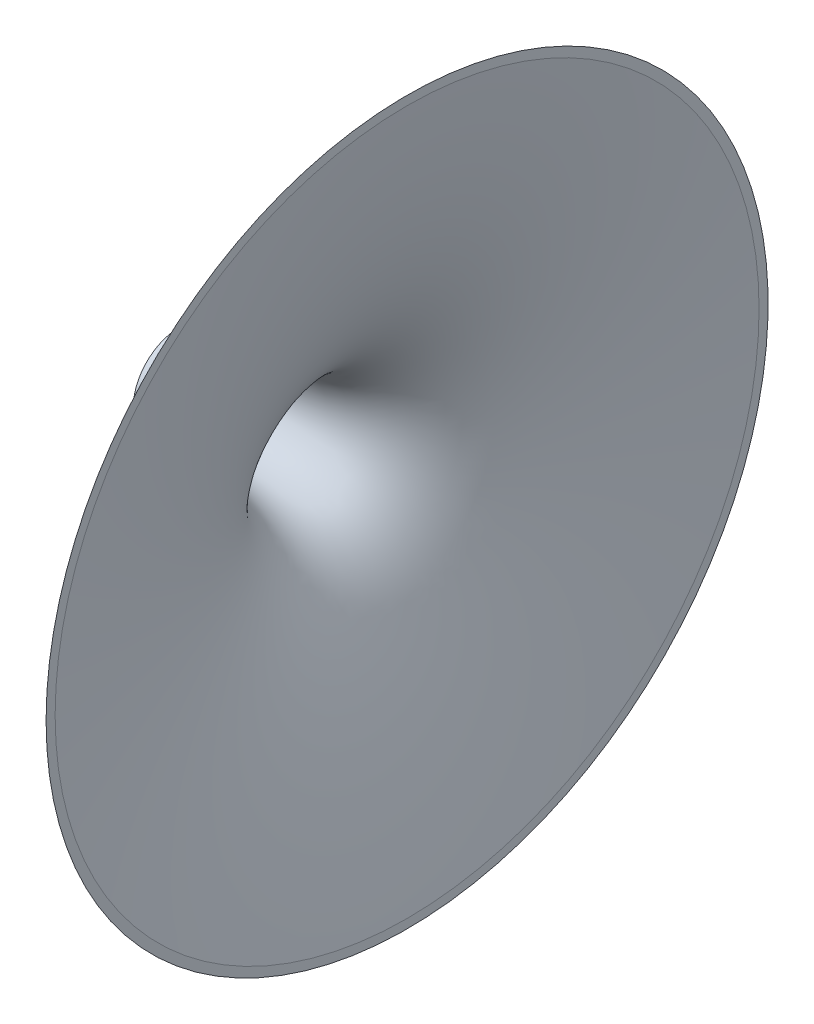
SolidWorks part; units mm, degrees
ref_plane "Front Plane" through (0, 0, 0) normal (0, 0, 1) x (1, 0, 0)
ref_plane "Top Plane" through (0, 0, 0) normal (0, 1, 0) x (1, 0, 0)
ref_plane "Right Plane" through (0, 0, 0) normal (1, 0, 0) x (0, 0, -1)
sketch "Sketch7" plane through (0, 0, 0) normal (0, 0, 1) x (1, 0, 0)
  line L0 (0, 0) -> (62.8319, 0) construction
  line L1 (0, 12.8183) -> (0, 10.3183)
  line L2 (62.8319, 99.7042) -> (62.8319, 97.2042)
  spline S0 degree 4 poles (-6.2852, 12.6815) (-6.0802, 12.685) (-5.6807, 12.6917) (-4.9676, 12.7033) (-3.6152, 12.7307) (-2.5556, 12.7512) (-0.6387, 12.8001) (0.2683, 12.8253) (1.7229, 12.8702) (2.754, 12.9064) (4.1738, 12.9604) (5.8195, 13.0323) (7.713, 13.129) (9.8066, 13.2591) (12.344, 13.4483) (14.8721, 13.6858) (17.4555, 13.9941) (20.0348, 14.3917) (22.1229, 14.781) (24.3759, 15.2858) (26.7822, 15.9449) (29.2039, 16.7757) (31.5994, 17.8109) (33.7417, 18.9446) (35.6358, 20.1379) (37.4207, 21.4637) (39.2171, 23.0224) (41.0429, 24.8799) (42.8548, 27.0548) (44.8353, 29.8598) (46.8164, 33.2141) (48.8445, 37.3182) (51.173, 42.9994) (53.1091, 48.8409) (54.7684, 54.7628) (56.1586, 60.4539) (57.1752, 65.0272) (58.1108, 69.6208) (58.9763, 74.2226) (59.6819, 78.2674) (60.2521, 81.7259) (60.7101, 84.6335) (61.0602, 86.9215) (61.41, 89.2918) (61.7314, 91.5196) (62.0751, 93.9965) (62.3544, 96.0424) (62.7539, 99.0868) (62.9812, 100.865) (63.4494, 104.6082) (63.6799, 106.5737) (63.9997, 109.2655) (64.1382, 110.5067) (64.2374, 111.3672) (64.278, 111.729) knots 0 0 0 0 0 0.00556 0.01112 0.022241 0.033361 0.044481 0.052341 0.060202 0.068062 0.075923 0.091644 0.107365 0.12142 0.135475 0.163586 0.179306 0.195027 0.209364 0.223701 0.244662 0.265623 0.281777 0.297498 0.313219 0.32894 0.344661 0.364768 0.386877 0.408987 0.441775 0.474939 0.516364 0.582692 0.615856 0.64902 0.682184 0.715348 0.748512 0.781676 0.798259 0.814841 0.831423 0.848006 0.864588 0.88117 0.897752 0.914335 0.935751 0.957167 0.978584 0.989292 1 1 1 1 1 construction
  spline S1 degree 4 poles (0, 12.8183) (0.2414, 12.8252) (0.7344, 12.8397) (1.7229, 12.8702) (2.754, 12.9064) (4.1738, 12.9604) (5.8195, 13.0323) (7.713, 13.129) (9.8066, 13.2591) (12.344, 13.4483) (14.8721, 13.6858) (17.4555, 13.9941) (20.0348, 14.3917) (22.1229, 14.781) (24.3759, 15.2858) (26.7822, 15.9449) (29.2039, 16.7757) (31.5994, 17.8109) (33.7417, 18.9446) (35.6358, 20.1379) (37.4207, 21.4637) (39.2171, 23.0224) (41.0429, 24.8799) (42.8548, 27.0548) (44.8353, 29.8598) (46.8164, 33.2141) (48.8445, 37.3182) (51.173, 42.9994) (53.1091, 48.8409) (54.7684, 54.7628) (56.1586, 60.4539) (57.1752, 65.0272) (58.1108, 69.6208) (58.9763, 74.2226) (59.6819, 78.2674) (60.2521, 81.7259) (60.7101, 84.6335) (61.0602, 86.9215) (61.41, 89.2918) (61.7314, 91.5196) (62.0751, 93.9965) (62.3544, 96.0424) (62.6337, 98.1706) (62.767, 99.1988) (62.8319, 99.7042) knots 0.044481 0.044481 0.044481 0.044481 0.044481 0.052341 0.060202 0.068062 0.075923 0.091644 0.107365 0.12142 0.135475 0.163586 0.179306 0.195027 0.209364 0.223701 0.244662 0.265623 0.281777 0.297498 0.313219 0.32894 0.344661 0.364768 0.386877 0.408987 0.441775 0.474939 0.516364 0.582692 0.615856 0.64902 0.682184 0.715348 0.748512 0.781676 0.798259 0.814841 0.831423 0.848006 0.864588 0.88117 0.897752 0.914335 0.914335 0.914335 0.914335 0.914335
  spline S2 degree 4 poles (-6.2852, 10.1815) (-6.0802, 10.185) (-5.6807, 10.1917) (-4.9676, 10.2033) (-3.6152, 10.2307) (-2.5556, 10.2512) (-0.6387, 10.3001) (0.2683, 10.3253) (1.7229, 10.3702) (2.754, 10.4064) (4.1738, 10.4604) (5.8195, 10.5323) (7.713, 10.629) (9.8066, 10.7591) (12.344, 10.9483) (14.8721, 11.1858) (17.4555, 11.4941) (20.0348, 11.8917) (22.1229, 12.281) (24.3759, 12.7858) (26.7822, 13.4449) (29.2039, 14.2757) (31.5994, 15.3109) (33.7417, 16.4446) (35.6358, 17.6379) (37.4207, 18.9637) (39.2171, 20.5224) (41.0429, 22.3799) (42.8548, 24.5548) (44.8353, 27.3598) (46.8164, 30.7141) (48.8445, 34.8182) (51.173, 40.4994) (53.1091, 46.3409) (54.7684, 52.2628) (56.1586, 57.9539) (57.1752, 62.5272) (58.1108, 67.1208) (58.9763, 71.7226) (59.6819, 75.7674) (60.2521, 79.2259) (60.7101, 82.1335) (61.0602, 84.4215) (61.41, 86.7918) (61.7314, 89.0196) (62.0751, 91.4965) (62.3544, 93.5424) (62.7539, 96.5868) (62.9812, 98.365) (63.4494, 102.1082) (63.6799, 104.0737) (63.9997, 106.7655) (64.1382, 108.0067) (64.2374, 108.8672) (64.278, 109.229) knots 0 0 0 0 0 0.00556 0.01112 0.022241 0.033361 0.044481 0.052341 0.060202 0.068062 0.075923 0.091644 0.107365 0.12142 0.135475 0.163586 0.179306 0.195027 0.209364 0.223701 0.244662 0.265623 0.281777 0.297498 0.313219 0.32894 0.344661 0.364768 0.386877 0.408987 0.441775 0.474939 0.516364 0.582692 0.615856 0.64902 0.682184 0.715348 0.748512 0.781676 0.798259 0.814841 0.831423 0.848006 0.864588 0.88117 0.897752 0.914335 0.935751 0.957167 0.978584 0.989292 1 1 1 1 1 construction
  spline S3 degree 4 poles (0, 10.3183) (0.2414, 10.3252) (0.7344, 10.3397) (1.7229, 10.3702) (2.754, 10.4064) (4.1738, 10.4604) (5.8195, 10.5323) (7.713, 10.629) (9.8066, 10.7591) (12.344, 10.9483) (14.8721, 11.1858) (17.4555, 11.4941) (20.0348, 11.8917) (22.1229, 12.281) (24.3759, 12.7858) (26.7822, 13.4449) (29.2039, 14.2757) (31.5994, 15.3109) (33.7417, 16.4446) (35.6358, 17.6379) (37.4207, 18.9637) (39.2171, 20.5224) (41.0429, 22.3799) (42.8548, 24.5548) (44.8353, 27.3598) (46.8164, 30.7141) (48.8445, 34.8182) (51.173, 40.4994) (53.1091, 46.3409) (54.7684, 52.2628) (56.1586, 57.9539) (57.1752, 62.5272) (58.1108, 67.1208) (58.9763, 71.7226) (59.6819, 75.7674) (60.2521, 79.2259) (60.7101, 82.1335) (61.0602, 84.4215) (61.41, 86.7918) (61.7314, 89.0196) (62.0751, 91.4965) (62.3544, 93.5424) (62.6337, 95.6706) (62.767, 96.6988) (62.8319, 97.2042) knots 0.044481 0.044481 0.044481 0.044481 0.044481 0.052341 0.060202 0.068062 0.075923 0.091644 0.107365 0.12142 0.135475 0.163586 0.179306 0.195027 0.209364 0.223701 0.244662 0.265623 0.281777 0.297498 0.313219 0.32894 0.344661 0.364768 0.386877 0.408987 0.441775 0.474939 0.516364 0.582692 0.615856 0.64902 0.682184 0.715348 0.748512 0.781676 0.798259 0.814841 0.831423 0.848006 0.864588 0.88117 0.897752 0.914335 0.914335 0.914335 0.914335 0.914335
  point P7 (0, 0)
  point P12 (0, 0)
  point P13 (0, 0)
  point P14 (0, 0)
  point P15 (0, 0)
  point P16 (0, 0)
  point P17 (0, 0)
  point P18 (0, 0)
revolve "Revolve1" add sketch "Sketch7" angle 360 about L0
